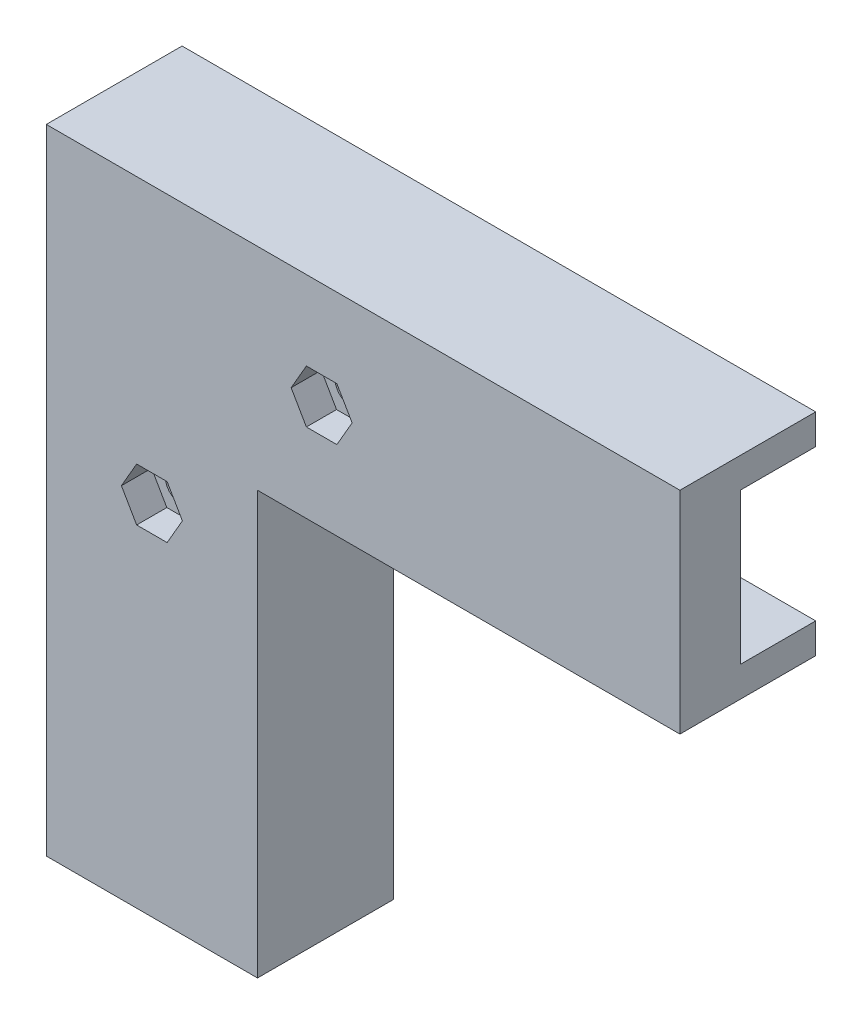
SolidWorks part; units mm, degrees
ref_plane "Plan de face" through (0, 0, 0) normal (0, 0, 1) x (1, 0, 0)
ref_plane "Plan de dessus" through (0, 0, 0) normal (0, 1, 0) x (1, 0, 0)
ref_plane "Plan de droite" through (0, 0, 0) normal (1, 0, 0) x (0, 0, -1)
sketch "Esquisse1" plane through (0, 0, 0) normal (0, 0, 1) x (1, 0, 0)
  line L0 (0, 0) -> (0, 60)
  line L1 (0, 60) -> (60, 60)
  line L2 (60, 60) -> (60, 80)
  line L3 (60, 80) -> (-20, 80)
  line L4 (-20, 80) -> (-20, 0)
  line L5 (-20, 0) -> (0, 0)
  dimension "D1" = 60
  dimension "D2" = 60
  dimension "D3" = 20
  dimension "D4" = 20
extrude "Boss.-Extru.1" add sketch "Esquisse1" along normal blind 8
sketch "Esquisse2" plane through (0, 0, 8) normal (0, 0, 1) x (1, 0, 0)
  line L0 (-12.0207, 51) -> (-7.9793, 44) construction
  line L1 (-20, 80) -> (-20, 0) construction
  line L3 (-5.9585, 47.5) -> (-14.0415, 47.5) construction
  line L5 (60, 80) -> (-20, 80) construction
  line L6 (0, 0) -> (0, 60) construction
  line L7 (-14.0415, 47.5) -> (-12.0207, 51)
  line L8 (-12.0207, 51) -> (-7.9793, 51)
  line L9 (-7.9793, 51) -> (-5.9585, 47.5)
  line L10 (-5.9585, 47.5) -> (-7.9793, 44)
  line L11 (-7.9793, 44) -> (-12.0207, 44)
  line L12 (-12.0207, 44) -> (-14.0415, 47.5)
  line L13 (10.4793, 66.5) -> (14.5207, 73.5) construction
  line L14 (16.5415, 70) -> (8.4585, 70) construction
  line L15 (-5.9585, 47.5) -> (-6.29, 47.0056)
  line L20 (-12.0207, 44) -> (-12.0207, 51) construction
  line L23 (8.4585, 70) -> (10.4793, 73.5)
  line L24 (10.4793, 73.5) -> (14.5207, 73.5)
  line L25 (14.5207, 73.5) -> (16.5415, 70)
  line L26 (16.5415, 70) -> (14.5207, 66.5)
  line L27 (14.5207, 66.5) -> (10.4793, 66.5)
  line L28 (10.4793, 66.5) -> (8.4585, 70)
  line L31 (16.5415, 70) -> (16.21, 69.5056)
  line L36 (10.4793, 66.5) -> (10.4793, 73.5) construction
  point P26 (-10, 47.5)
  point P27 (12.5, 70)
  dimension "D2" = 32.5
  dimension "D3" = 7
  dimension "D4" = 7
  dimension "D6" = 120
  dimension "D7" = 30
  dimension "D8" = 7
  dimension "D9" = 7
  dimension "D10" = 7
  dimension "D11" = 120
  dimension "D12" = 30
  dimension "D13" = 10
  dimension "D14" = 10
  dimension "D15" = 32.5
extrude "Enlèv. mat.-Extru.1" cut sketch "Esquisse2" against normal blind 4
sketch "Esquisse3" plane through (0, 0, 4) normal (0, 0, 1) x (1, 0, 0)
  line L0 (-7.9793, 51) -> (-5.9585, 47.5) construction
  line L1 (-14.0415, 47.5) -> (-12.0207, 51) construction
  line L3 (10.4793, 73.5) -> (14.5207, 73.5) construction
  line L4 (16.5415, 70) -> (14.5207, 66.5) construction
  circle A0 centre (-10, 47.5) radius 2.25
  circle A1 centre (12.5, 70) radius 2.25
  dimension "D1" = 3.5
  dimension "D2" = 3.5
  dimension "D3" = 4.5
  dimension "D4" = 4.5
  dimension "D5" = 3.5
  dimension "D6" = 3.5
extrude "Enlèv. mat.-Extru.2" cut sketch "Esquisse3" against normal through all
sketch "Esquisse4" plane through (0, 0, 8) normal (0, 0, 1) x (1, 0, 0)
  line L0 (0, 0) -> (0, 60)
  line L2 (0, 60) -> (60, 60)
  line L3 (60, 60) -> (60, 56)
  line L4 (60, 56) -> (4, 56)
  line L5 (4, 56) -> (4, 0)
  line L6 (4, 0) -> (0, 0)
  line L7 (60, 80) -> (60, 84)
  line L8 (60, 84) -> (-24, 84)
  line L9 (-24, 84) -> (-24, 0)
  line L10 (-24, 0) -> (-20, 0)
  line L11 (-20, 0) -> (-20, 80)
  line L12 (-20, 80) -> (60, 80)
  dimension "D1" = 4
  dimension "D2" = 4
  dimension "D3" = 4
  dimension "D4" = 4
extrude "Boss.-Extru.2" add sketch "Esquisse4" against normal blind 18
fillet "Congé1" radius 6 1 edges at (0, 60, -5)
